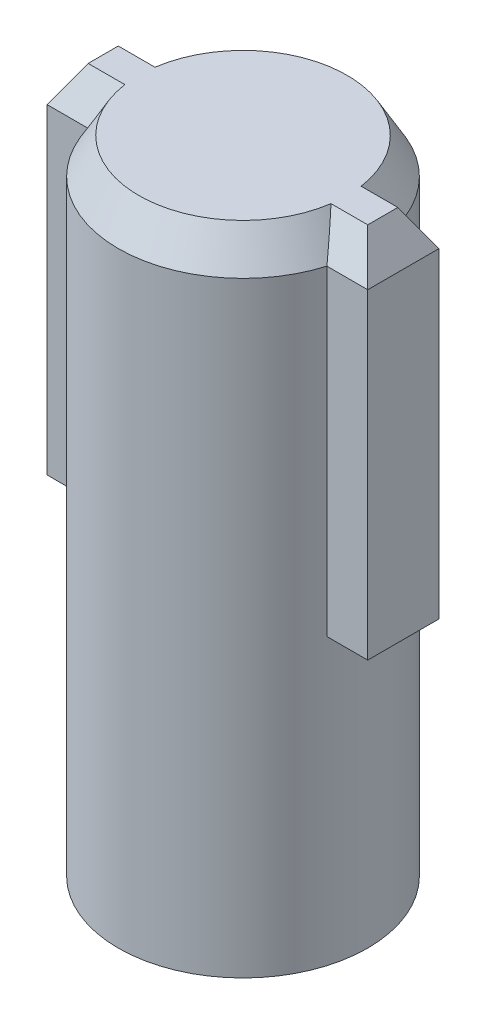
SolidWorks part; units mm, degrees
ref_plane "Спереди" through (0, 0, 0) normal (0, 0, 1) x (1, 0, 0)
ref_plane "Сверху" through (0, 0, 0) normal (0, 1, 0) x (1, 0, 0)
ref_plane "Справа" through (0, 0, 0) normal (1, 0, 0) x (0, 0, -1)
sketch "Sketch1" plane through (0, 0, 0) normal (0, 1, 0) x (1, 0, 0)
  circle A0 centre (0, 0) radius 3.5
  dimension "D1" = 7
extrude "Boss-Extrude1" add sketch "Sketch1" along normal blind 18
sketch "Sketch2" plane through (0, 18, 0) normal (0, 1, 0) x (1, 0, 0)
  line L1 (4.5, 1) -> (-4.5, 1)
  line L2 (4.5, 1) -> (4.5, -1)
  line L3 (4.5, -1) -> (-4.5, -1)
  line L4 (-4.5, 1) -> (-4.5, -1)
  line L5 (4.5, 1) -> (-4.5, -1) construction
  line L6 (4.5, -1) -> (-4.5, 1) construction
  point P0 (0, 0)
  dimension "D1" = 2
  dimension "D2" = 9
extrude "Boss-Extrude3" add sketch "Sketch2" against normal blind 10
sketch "Sketch3" plane through (0, 0, 0) normal (0, -1, 0) x (1, 0, 0)
  line L0 (3.3541, -1) -> (-3.3541, -1) construction
  line L1 (-3.5, 0) -> (3.5, 0) construction
  line L2 (4.5, -1) -> (3.3541, -1) construction
  line L3 (-5, -1) -> (5, -1)
  line L4 (-5, -1) -> (-5, -3.5)
  line L5 (-5, -3.5) -> (5, -3.5)
  line L6 (5, -1) -> (5, -3.5)
  line L7 (-5, -1) -> (5, -3.5) construction
  line L8 (-5, -3.5) -> (5, -1) construction
  circle A0 centre (0, 0) radius 3.5 construction
  point P7 (0, -2.25)
  point P12 (0, -1)
  point P13 (0, -1)
  point P16 (0, -3.5)
  dimension "D2" = 10
extrude "Cut-Extrude3" cut sketch "Sketch3" against normal blind 4 from offset 8 offset against normal yes
chamfer "Chamfer1" distance 1 angle 30 8 edges at (-3.9271, 18, 1) (-4.5, 18, 0) (-3.9271, 18, -1) (0, 18, -3.5) (3.9271, 18, -1) (4.5, 18, 0) (3.9271, 18, 1) (0, 18, 3.5)
